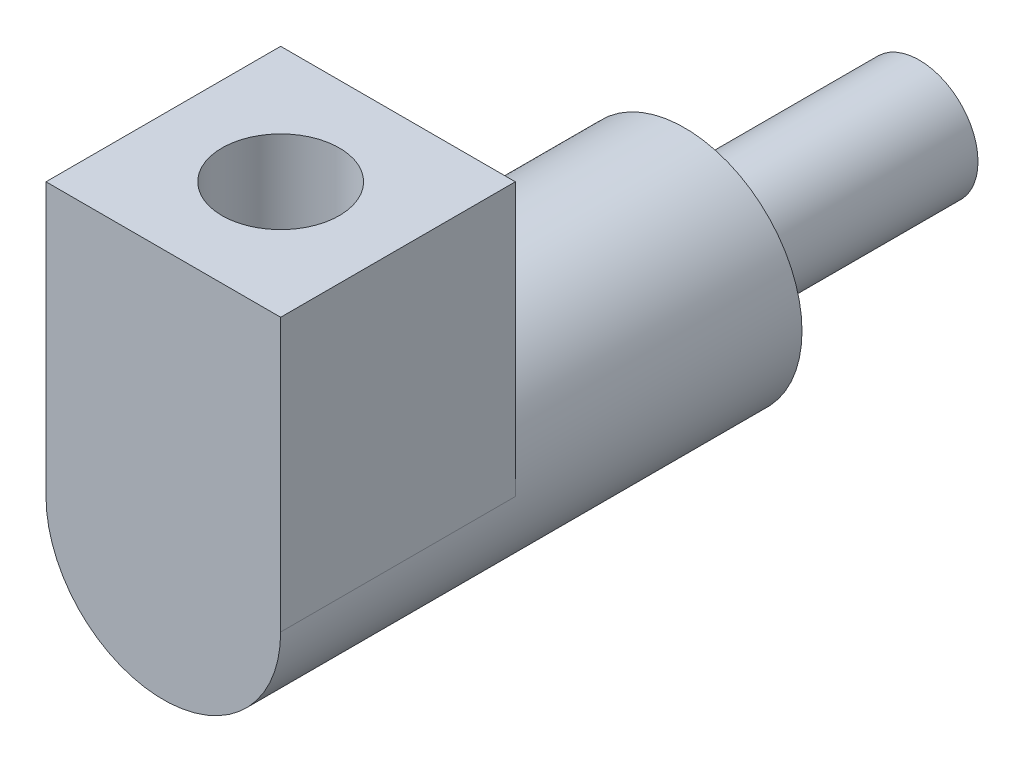
SolidWorks part; units mm, degrees
ref_plane "Front Plane" through (0, 0, 0) normal (0, 0, 1) x (1, 0, 0)
ref_plane "Top Plane" through (0, 0, 0) normal (0, 1, 0) x (1, 0, 0)
ref_plane "Right Plane" through (0, 0, 0) normal (1, 0, 0) x (0, 0, -1)
sketch "sketch1_link4" plane through (0, 0, 0) normal (0, 0, 1) x (1, 0, 0)
  circle A0 centre (0, 0) radius 15
  dimension "D1" = 30
extrude "Boss-Extrude1" add sketch "sketch1_link4" along normal mid plane 60
sketch "sketch2_link4" plane through (0, 0, 30) normal (0, 0, 1) x (1, 0, 0)
  circle A0 centre (0, 0) radius 30
  dimension "D1" = 60
extrude "Boss-Extrude2" add sketch "sketch2_link4" along normal blind 73.3
sketch "sketch3_link4" plane through (0, 0, 103.3) normal (0, 0, 1) x (1, 0, 0)
  line L0 (-30, 0) -> (-30, 69.7)
  line L1 (30, 0) -> (30, 69.7)
  line L2 (-30, 69.7) -> (30, 69.7)
  arc A0 (30, 0) -> (-30, 0) centre (0, 0) cw
  dimension "D1" = 30
  dimension "D2" = 69.7
extrude "Boss-Extrude3" add sketch "sketch3_link4" along normal blind 60
sketch "sketch4_link4" plane through (0, 69.7, 0) normal (0, 1, 0) x (1, 0, 0)
  line L0 (-30, -103.3) -> (30, -163.3) construction
  circle A0 centre (0, -133.3) radius 15
  dimension "D1" = 30
extrude "Cut-Extrude1" cut sketch "sketch4_link4" against normal blind 30
